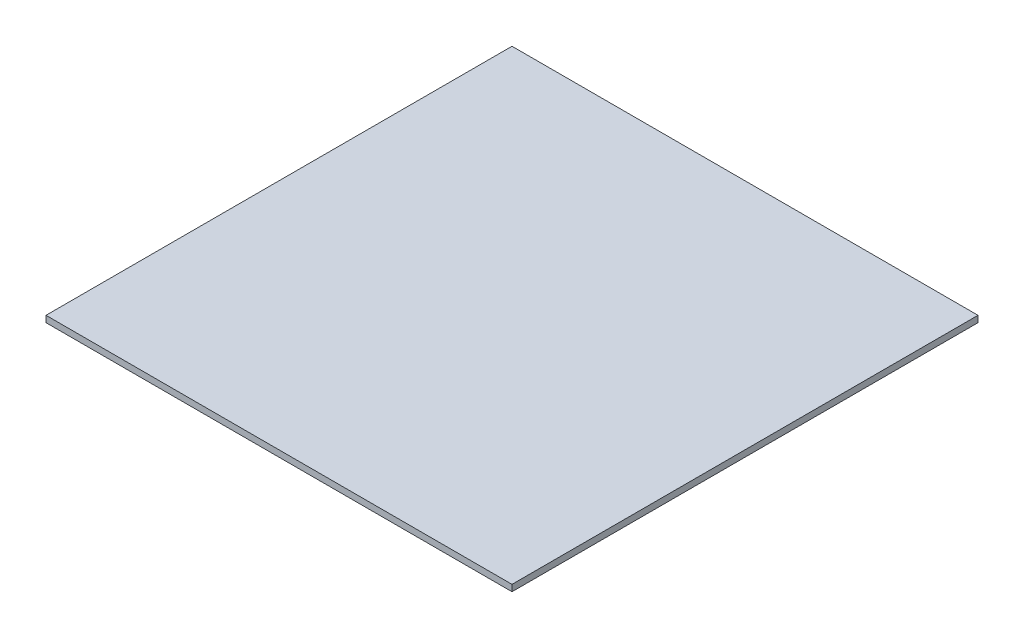
SolidWorks part; units mm, degrees
material "Glass"
ref_plane "Front Plane" through (0, 0, 0) normal (0, 0, 1) x (1, 0, 0)
ref_plane "Top Plane" through (0, 0, 0) normal (0, 1, 0) x (1, 0, 0)
ref_plane "Right Plane" through (0, 0, 0) normal (1, 0, 0) x (0, 0, -1)
sketch "Sketch1" plane through (0, 0, 0) normal (0, 1, 0) x (1, 0, 0)
  line L1 (203.2, 203.2) -> (-203.2, 203.2)
  line L2 (203.2, 203.2) -> (203.2, -203.2)
  line L3 (203.2, -203.2) -> (-203.2, -203.2)
  line L4 (-203.2, 203.2) -> (-203.2, -203.2)
  line L5 (203.2, 203.2) -> (-203.2, -203.2) construction
  line L6 (203.2, -203.2) -> (-203.2, 203.2) construction
  point P0 (0, 0)
  dimension "D1" = 406.4
extrude "Boss-Extrude1" add sketch "Sketch1" along normal blind 5.6
